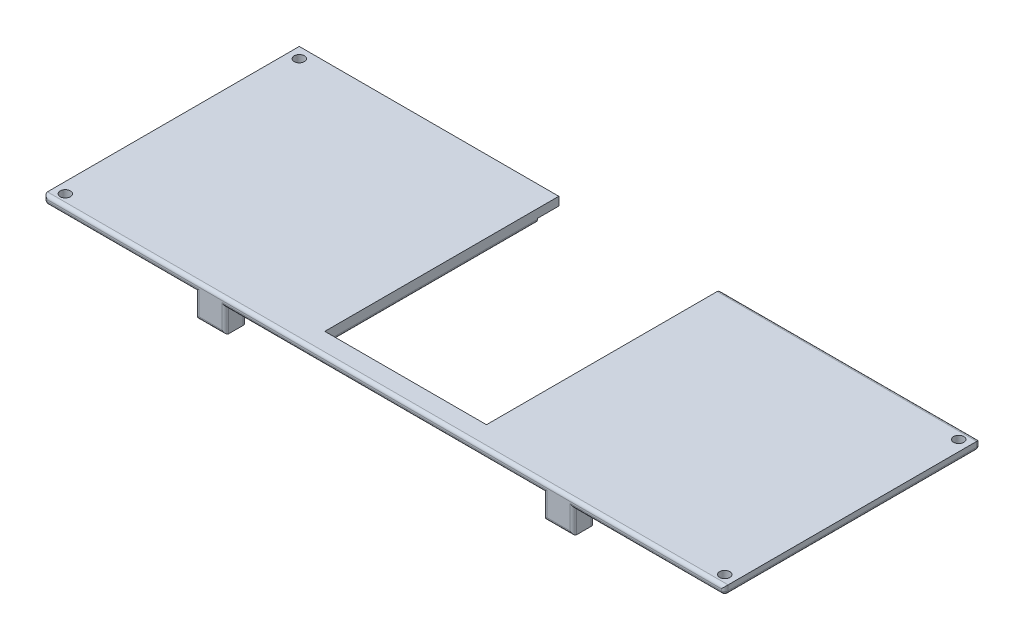
SolidWorks part; units mm, degrees
ref_plane "Front Plane" through (0, 0, 0) normal (0, 0, 1) x (1, 0, 0)
ref_plane "Top Plane" through (0, 0, 0) normal (0, 1, 0) x (1, 0, 0)
ref_plane "Right Plane" through (0, 0, 0) normal (1, 0, 0) x (0, 0, -1)
sketch "Sketch1" plane through (0, 0, 0) normal (0, 1, 0) x (1, 0, 0)
  line L54 (10, 30) -> (12, 30)
  line L58 (-12, 30) -> (-10, 30)
  line L60 (-25.23, 30) -> (-22.2, 30)
  line L64 (22.2, 30) -> (25.23, 30)
  line L68 (25.23, 0) -> (22.2, 0)
  line L72 (-22.2, 0) -> (-25.23, 0)
  line L76 (-18.7, 2.5) -> (-18.7, 0)
  line L77 (-18.7, 0) -> (18.7, 0)
  line L78 (18.7, 0) -> (18.7, 2.5)
  line L79 (18.7, 2.5) -> (-18.7, 2.5)
  line L80 (22.2, 2.5) -> (22.2, 0)
  line L81 (22.2, 0) -> (40, 0)
  line L82 (40, 0) -> (40, 30)
  line L83 (40, 30) -> (22.2, 30)
  line L84 (22.2, 30) -> (22.2, 27.5)
  line L85 (22.2, 27.5) -> (37.5, 27.5)
  line L86 (37.5, 27.5) -> (37.5, 2.5)
  line L87 (37.5, 2.5) -> (22.2, 2.5)
  line L88 (9.5, 30) -> (9.5, 27.5)
  line L89 (9.5, 27.5) -> (18.7, 27.5)
  line L90 (18.7, 27.5) -> (18.7, 30)
  line L91 (18.7, 30) -> (9.5, 30)
  line L92 (-18.7, 27.5) -> (-9.5, 27.5)
  line L93 (-9.5, 27.5) -> (-9.5, 30)
  line L94 (-9.5, 30) -> (-18.7, 30)
  line L95 (-18.7, 30) -> (-18.7, 27.5)
  line L96 (-22.2, 27.5) -> (-22.2, 30)
  line L97 (-22.2, 30) -> (-40, 30)
  line L98 (-40, 30) -> (-40, 0)
  line L99 (-40, 0) -> (-22.2, 0)
  line L100 (-22.2, 0) -> (-22.2, 2.5)
  line L101 (-22.2, 2.5) -> (-37.5, 2.5)
  line L102 (-37.5, 2.5) -> (-37.5, 27.5)
  line L103 (-37.5, 27.5) -> (-22.2, 27.5)
  circle A4 centre (-38.75, 1.25) radius 0.6
  circle A5 centre (-38.75, 28.75) radius 0.6
  circle A6 centre (38.75, 28.75) radius 0.6
  circle A7 centre (38.75, 1.25) radius 0.6
extrude "Boss-Extrude1" add sketch "Sketch1" against normal blind 1 contours L102 L103 L96 L60 L97 L98 L99 L72 L100 L101 A5 A4 | L78 L79 L76 L77 | L90 L91 L54 L88 L89 | L86 L87 L80 L68 L81 L82 L83 L64 L84 L85 A7 A6 | L94 L95 L92 L93
sketch "Sketch3" plane through (0, 0, 0) normal (0, 1, 0) x (1, 0, 0)
  line L0 (-22.2, 27.5) -> (-37.5, 27.5)
  line L1 (-9.5, 27.5) -> (-18.7, 27.5)
  line L2 (-9.5, 27.5) -> (-9.5, 2.5)
  line L3 (-9.5, 2.5) -> (-18.7, 2.5)
  line L4 (-37.5, 27.5) -> (-37.5, 2.5)
  line L5 (9.5, 27.5) -> (18.7, 27.5)
  line L6 (9.5, 27.5) -> (9.5, 2.5)
  line L7 (9.5, 2.5) -> (18.7, 2.5)
  line L8 (37.5, 27.5) -> (37.5, 2.5)
  line L9 (-18.7, 30) -> (-22.2, 30)
  line L10 (-18.7, 30) -> (-18.7, 27.5)
  line L12 (-22.2, 30) -> (-22.2, 27.5)
  line L13 (22.2, 30) -> (18.7, 30)
  line L14 (22.2, 30) -> (22.2, 27.5)
  line L16 (18.7, 30) -> (18.7, 27.5)
  line L18 (-18.7, 2.5) -> (-18.7, 0)
  line L19 (-18.7, 0) -> (-22.2, 0)
  line L20 (-22.2, 2.5) -> (-22.2, 0)
  line L22 (22.2, 2.5) -> (22.2, 0)
  line L23 (22.2, 0) -> (18.7, 0)
  line L24 (18.7, 2.5) -> (18.7, 0)
  line L25 (22.2, 27.5) -> (37.5, 27.5)
  line L26 (22.2, 2.5) -> (37.5, 2.5)
  line L27 (-22.2, 2.5) -> (-37.5, 2.5)
extrude "Boss-Extrude2" add sketch "Sketch3" against normal blind 1.5
sketch "Sketch4" plane through (0, 0, 0) normal (0, 1, 0) x (1, 0, 0)
  line L1 (-18.7, 30) -> (-22.2, 30)
  line L2 (-18.7, 30) -> (-18.7, 27.5)
  line L3 (-18.7, 27.5) -> (-22.2, 27.5)
  line L4 (-22.2, 30) -> (-22.2, 27.5)
  line L5 (22.2, 30) -> (18.7, 30)
  line L6 (22.2, 30) -> (22.2, 27.5)
  line L7 (22.2, 27.5) -> (18.7, 27.5)
  line L8 (18.7, 30) -> (18.7, 27.5)
  line L9 (-18.7, 2.5) -> (-22.2, 2.5)
  line L10 (-18.7, 2.5) -> (-18.7, 0)
  line L11 (-18.7, 0) -> (-22.2, 0)
  line L12 (-22.2, 2.5) -> (-22.2, 0)
  line L13 (22.2, 2.5) -> (18.7, 2.5)
  line L14 (22.2, 2.5) -> (22.2, 0)
  line L15 (22.2, 0) -> (18.7, 0)
  line L16 (18.7, 2.5) -> (18.7, 0)
extrude "Boss-Extrude3" add sketch "Sketch4" against normal blind 3.8
sketch "Sketch5" plane through (0, 0, 0) normal (0, 1, 0) x (1, 0, 0)
  line L52 (-10, 31.6366) -> (10, 31.6366)
  line L53 (10, 31.6366) -> (10, 30)
  line L54 (10, 30) -> (12, 30)
  line L55 (12, 30) -> (12, 33.8944)
  line L56 (12, 33.8944) -> (-12, 33.8944)
  line L57 (-12, 33.8944) -> (-12, 30)
  line L58 (-12, 30) -> (-10, 30)
  line L59 (-10, 30) -> (-10, 31.6366)
  line L60 (-25.23, 30) -> (-22.2, 30)
  line L61 (-22.2, 30) -> (-22.2, 32)
  line L62 (-22.2, 32) -> (-25.23, 32)
  line L63 (-25.23, 32) -> (-25.23, 30)
  line L64 (22.2, 30) -> (25.23, 30)
  line L65 (25.23, 30) -> (25.23, 32)
  line L66 (25.23, 32) -> (22.2, 32)
  line L67 (22.2, 32) -> (22.2, 30)
  line L68 (25.23, 0) -> (22.2, 0)
  line L69 (22.2, 0) -> (22.2, -2)
  line L70 (22.2, -2) -> (25.23, -2)
  line L71 (25.23, -2) -> (25.23, 0)
  line L72 (-22.2, 0) -> (-25.23, 0)
  line L73 (-25.23, 0) -> (-25.23, -2)
  line L74 (-25.23, -2) -> (-22.2, -2)
  line L75 (-22.2, -2) -> (-22.2, 0)
  line L76 (-18.7, 2.5) -> (-18.7, 0)
  line L77 (-18.7, 0) -> (18.7, 0)
  line L78 (18.7, 0) -> (18.7, 2.5)
  line L79 (18.7, 2.5) -> (-18.7, 2.5)
  line L80 (22.2, 2.5) -> (22.2, 0)
  line L81 (22.2, 0) -> (40, 0)
  line L82 (40, 0) -> (40, 30)
  line L83 (40, 30) -> (22.2, 30)
  line L84 (22.2, 30) -> (22.2, 27.5)
  line L85 (22.2, 27.5) -> (37.5, 27.5)
  line L86 (37.5, 27.5) -> (37.5, 2.5)
  line L87 (37.5, 2.5) -> (22.2, 2.5)
  line L88 (9.5, 30) -> (9.5, 27.5)
  line L89 (9.5, 27.5) -> (18.7, 27.5)
  line L90 (18.7, 27.5) -> (18.7, 30)
  line L91 (18.7, 30) -> (9.5, 30)
  line L92 (-18.7, 27.5) -> (-9.5, 27.5)
  line L93 (-9.5, 27.5) -> (-9.5, 30)
  line L94 (-9.5, 30) -> (-18.7, 30)
  line L95 (-18.7, 30) -> (-18.7, 27.5)
  line L96 (-22.2, 27.5) -> (-22.2, 30)
  line L97 (-22.2, 30) -> (-40, 30)
  line L98 (-40, 30) -> (-40, 0)
  line L99 (-40, 0) -> (-22.2, 0)
  line L100 (-22.2, 0) -> (-22.2, 2.5)
  line L101 (-22.2, 2.5) -> (-37.5, 2.5)
  line L102 (-37.5, 2.5) -> (-37.5, 27.5)
  line L103 (-37.5, 27.5) -> (-22.2, 27.5)
  circle A4 centre (-38.75, 1.25) radius 0.6
  circle A5 centre (-38.75, 28.75) radius 0.6
  circle A6 centre (38.75, 28.75) radius 0.6
  circle A7 centre (38.75, 1.25) radius 0.6
fillet "Fillet1" radius 0.4 37 edges at (-22.2, -2.65, -27.5) (-18.7, -2.65, -27.5) (-18.7, -2.4, -30) (-22.2, -2.4, -30) (14.1, -1, -30) (18.7, -2.4, -30) (20.45, -3.8, -30) (22.2, -2.4, -30) (31.1, -1, -30) (40, -0.5, -30) (24.75, 0, -30) (9.5, -0.5, -30) (-18.7, -2.4, 0) (-20.45, -3.8, 0) (-22.2, -2.4, 0) (-31.1, -1, 0) (-40, -0.5, 0) (0, 0, 0) (40, -0.5, 0) (31.1, -1, 0) (22.2, -2.4, 0) (20.45, -3.8, 0) (18.7, -2.4, 0) (0, -1, 0) (-40, -1, -15) (0, -1, -2.5) (9.5, -1.5, -15) (-9.5, -1.5, -15) (40, -1, -15) (37.5, -1.5, -15) (-37.5, -1.5, -15) (-18.7, -2.65, -2.5) (-22.2, -2.65, -2.5) (18.7, -2.65, -2.5) (22.2, -2.65, -2.5) (22.2, -2.65, -27.5) (18.7, -2.65, -27.5)
